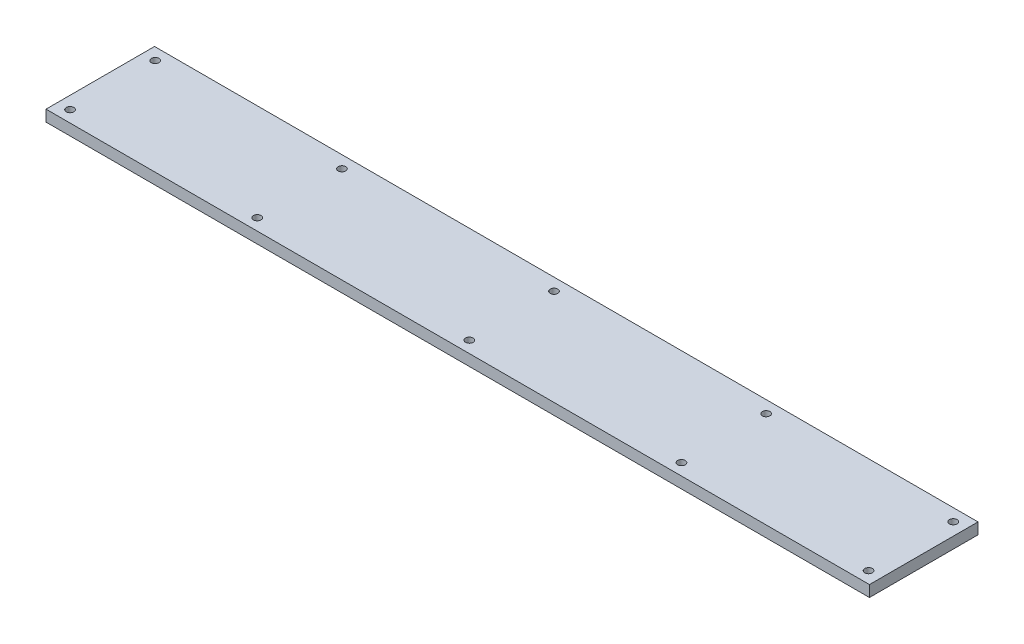
SolidWorks part; units mm, degrees
ref_plane "Front Plane" through (0, 0, 0) normal (0, 0, 1) x (1, 0, 0)
ref_plane "Top Plane" through (0, 0, 0) normal (0, 1, 0) x (1, 0, 0)
ref_plane "Right Plane" through (0, 0, 0) normal (1, 0, 0) x (0, 0, -1)
sketch "Sketch1" plane through (0, 0, 0) normal (0, 1, 0) x (1, 0, 0)
  line L1 (0, 0) -> (-330, 0)
  line L2 (0, 0) -> (0, 43.5)
  line L3 (0, 43.5) -> (-330, 43.5)
  line L4 (-330, 0) -> (-330, 43.5)
  dimension "D1" = 330
  dimension "D2" = 43.5
extrude "Boss-Extrude1" add sketch "Sketch1" along normal blind 4.5
hole_wizard "#31 (0.12) Diameter Hole3" positions "Sketch7" profile "Sketch6" hole size "#31" standard "ANSI Inch" end condition through all
sketch "Sketch7" plane through (0, 4.5, 0) normal (0, 1, 0) x (1, 0, 0)
  line L0 (-330, 43.5) -> (-330, 0) construction
  line L2 (-330, 0) -> (0, 0) construction
  point P0 (-325, 38.75)
  point P2 (-325, 4.643)
  point P4 (-250, 4.643)
  point P6 (-250, 38.5918)
  point P8 (-165, 38.5918)
  point P10 (-165, 4.643)
  point P12 (-80, 4.643)
  point P14 (-80, 38.5918)
  point P16 (-5, 38.5918)
  point P18 (-5, 4.643)
  dimension "D1" = 38.75
  dimension "D2" = 5
  dimension "D4" = 80
  dimension "D5" = 165
  dimension "D7" = 250
  dimension "D8" = 325
sketch "Sketch6" plane through (-325, 4.5, -38.75) normal (1, 0, 0) x (0, 0, 1)
  line L0 (0, 0) -> (0, 4.5)
  line L1 (0, 4.5) -> (1.524, 4.5)
  line L2 (1.524, 4.5) -> (1.524, 0)
  line L5 (1.524, 0) -> (0, 0)
  line L11 (0, -6.35) -> (0, 107.95) construction
  dimension "Thru Hole Dia." = 3.048
  dimension "Thru Hole Depth" = 4.5
